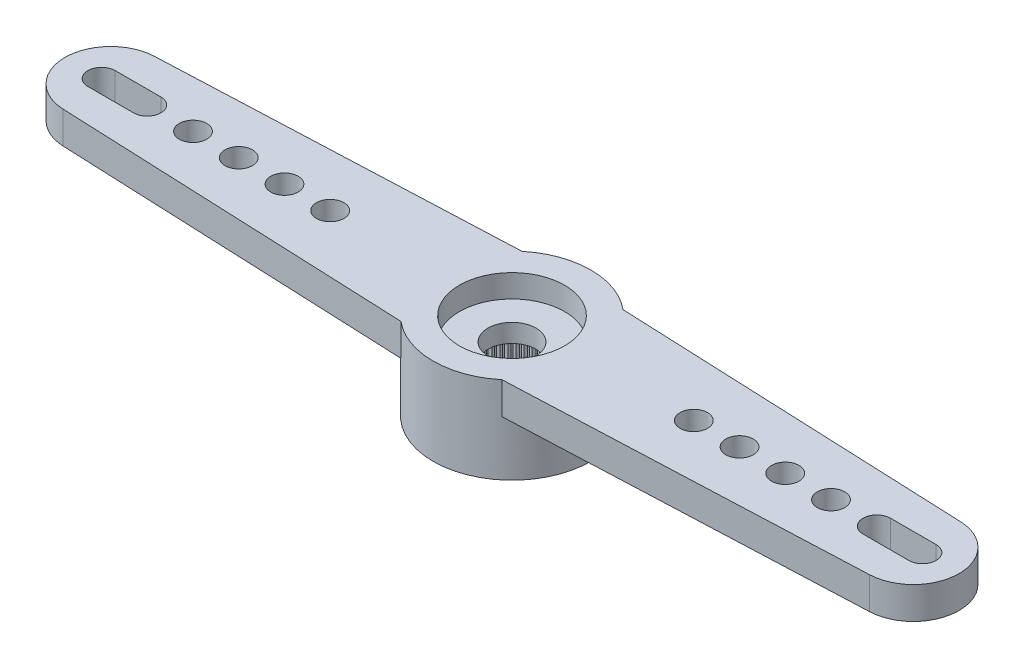
SolidWorks part; units mm, degrees
material "PVC Rígido"
ref_plane "Plano frontal" through (0, 0, 0) normal (0, 0, 1) x (1, 0, 0)
ref_plane "Plano superior" through (0, 0, 0) normal (0, 1, 0) x (1, 0, 0)
ref_plane "Plano direito" through (0, 0, 0) normal (1, 0, 0) x (0, 0, -1)
sketch "Esboço1" plane through (0, 0, 0) normal (0, 1, 0) x (1, 0, 0)
  line L0 (0, 0) -> (-17.55, 0) construction
  line L1 (-17.6344, 1.9982) -> (-2.2091, 2.65)
  line L2 (-2.2091, -2.65) -> (-17.6344, -1.9982)
  arc A0 (-2.2091, -2.65) -> (-2.2091, 2.65) centre (0, 0) ccw
  arc A1 (-17.6344, 1.9982) -> (-17.6344, -1.9982) centre (-17.55, 0) ccw
  dimension "D1" = 6.9
  dimension "D2" = 4
  dimension "D3" = 23
  dimension "D4" = 5.3
extrude "Ressalto-extrusão1" add sketch "Esboço1" against normal blind 1.4
sketch "Esboço2" plane through (0, -1.4, 0) normal (0, -1, 0) x (1, 0, 0)
  arc A0 (-2.2091, -2.65) -> (-2.2091, 2.65) centre (0, 0) ccw construction
  circle A1 centre (0, 0) radius 3.45
extrude "Ressalto-extrusão2" add sketch "Esboço2" along normal offset from surface (2.4 mm away) 3.8 up to face at (-8.9859, 0, 0)
hole_wizard "Furo4" positions "Esboço9" profile "Esboço10" legacy end condition through all
sketch "Esboço9" plane through (0, 0, 0) normal (0, 1, 0) x (1, 0, 0)
  line L1 (-17.95, 0) -> (0, 0) construction
  arc A2 (-17.6344, 1.9982) -> (-17.6344, -1.9982) centre (-17.55, 0) ccw construction
  point P0 (-17.95, 0)
  point P19 (-19.55, 0)
  dimension "D1" = 1.6
sketch "Esboço10" plane through (-17.95, 0, 0) normal (1, 0, 0) x (0, 0, 1)
  line L0 (0, 0) -> (0, 3.8)
  line L1 (0, 3.8) -> (0.6, 3.8)
  line L2 (0.6, 3.8) -> (0.6, 0)
  line L3 (0.6, 0) -> (0, 0)
  line L4 (0, 110) -> (0, -10) construction
  dimension "Diameter" = 1.2
  dimension "Depth" = 3.8
pattern_linear "Padrão linear1" count 6 spacing 2 along (1, 0, 0) of "Furo4"
pattern_circular "PadrãoCircular2" count 2 over 360 about axis through (0, 0, 0) along (0, 1, 0) of "Ressalto-extrusão1", "Furo4", "Padrão linear1"
hole_wizard "Furo1" positions "Esboço3" profile "Esboço4" legacy
sketch "Esboço3" plane through (0, -3.8, 0) normal (0, -1, 0) x (-1, 0, 0)
  point P0 (0, 0)
sketch "Esboço4" plane through (0, -3.8, 0) normal (1, 0, 0) x (0, 0, -1)
  line L0 (0, 0) -> (0, 2)
  line L1 (0, 2) -> (2.475, 2)
  line L2 (2.475, 2) -> (2.475, 0)
  line L3 (2.475, 0) -> (0, 0)
  line L4 (0, 110) -> (0, -10) construction
  dimension "Diameter" = 4.95
  dimension "Depth" = 2
hole_wizard "Furo2" positions "Esboço5" profile "Esboço6" legacy
sketch "Esboço5" plane through (0, 0, 0) normal (0, 1, 0) x (1, 0, 0)
  point P0 (0, 0)
sketch "Esboço6" plane through (0, 0, 0) normal (1, 0, 0) x (0, 0, 1)
  line L0 (0, 0) -> (0, 1)
  line L1 (0, 1) -> (2.3, 1)
  line L2 (2.3, 1) -> (2.3, 0)
  line L3 (2.3, 0) -> (0, 0)
  line L4 (0, 110) -> (0, -10) construction
  dimension "Diameter" = 4.6
  dimension "Depth" = 1
hole_wizard "Furo3" positions "Esboço7" profile "Esboço8" legacy end condition through all
sketch "Esboço7" plane through (0, 0, 0) normal (0, 1, 0) x (1, 0, 0)
  point P0 (0, 0)
sketch "Esboço8" plane through (0, 0, 0) normal (1, 0, 0) x (0, 0, 1)
  line L0 (0, 0) -> (0, 3.8)
  line L1 (0, 3.8) -> (1.05, 3.8)
  line L2 (1.05, 3.8) -> (1.05, 0)
  line L3 (1.05, 0) -> (0, 0)
  line L4 (0, 110) -> (0, -10) construction
  dimension "Diameter" = 2.1
  dimension "Depth" = 3.8
sketch "Esboço11" plane through (0, -3.8, 0) normal (0, -1, 0) x (1, 0, 0)
  line L0 (-0.0981, 2.4731) -> (0, 2.375)
  line L1 (0, 2.375) -> (0.0981, 2.4731)
  line L2 (0, 0) -> (0, 2.475) construction
  circle A0 centre (0, 0) radius 2.375 construction
  circle A1 centre (0, 0) radius 2.475
  arc A2 (0.0981, 2.4731) -> (-0.0981, 2.4731) centre (0, 0) ccw
  dimension "D3" = 4.75
  dimension "D2" = 0.1
  dimension "D1" = 0
extrude "Ressalto-extrusão3" add sketch "Esboço11" against normal up to surface (2 mm away) up to face at (0, -1.8, 1.05)
pattern_circular "PadrãoCircular1" count 60 over 360 about axis through (0, 0, 0) along (0, 1, 0) of "Ressalto-extrusão3"
sketch "Sketch1" plane through (0, 0, 0) normal (0, 1, 0) x (1, 0, 0)
  line L0 (-17.95, 0.6) -> (-15.95, 0.6)
  line L1 (-17.95, -0.6) -> (-15.95, -0.6)
  line L2 (15.95, 0.6) -> (17.95, 0.6)
  line L3 (17.95, 0.6) -> (17.95, -0.6)
  line L4 (17.95, -0.6) -> (15.95, -0.6)
  line L5 (15.95, -0.6) -> (15.95, 0.6)
  line L6 (-15.95, 0.6) -> (-15.95, -0.6)
  line L7 (-17.95, 0.6) -> (-17.95, -0.6)
  circle A0 centre (-17.95, 0) radius 0.6 construction
  circle A1 centre (-15.95, 0) radius 0.6 construction
  circle A2 centre (15.95, 0) radius 0.6 construction
  circle A3 centre (17.95, 0) radius 0.6 construction
extrude "Cut-Extrude1" cut sketch "Sketch1" against normal through all both and the other way through all
